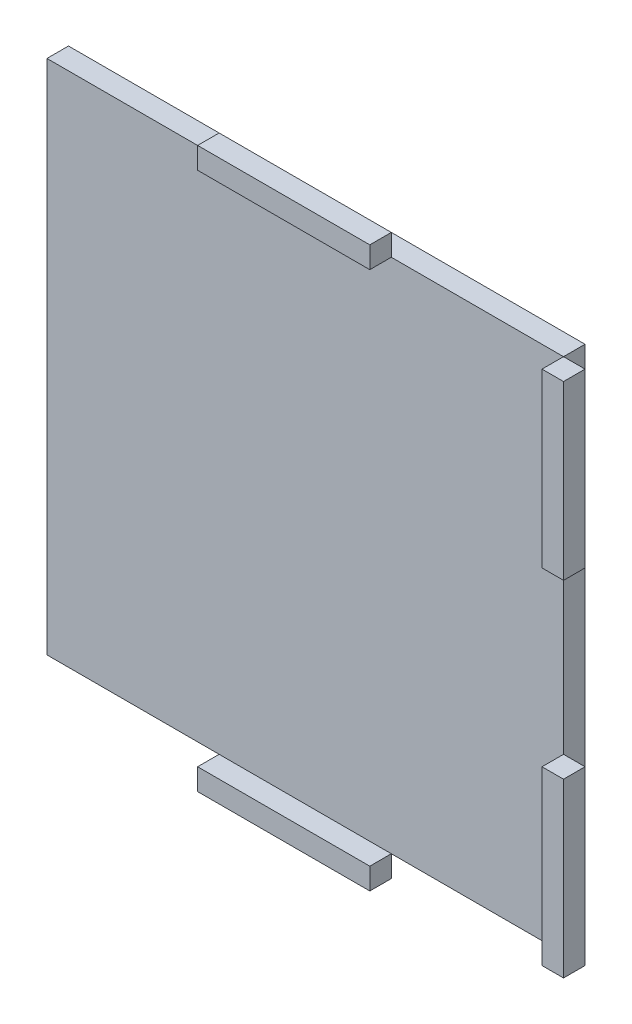
SolidWorks part; units mm, degrees
ref_plane "Front Plane" through (0, 0, 0) normal (0, 0, 1) x (1, 0, 0)
ref_plane "Top Plane" through (0, 0, 0) normal (0, 1, 0) x (1, 0, 0)
ref_plane "Right Plane" through (0, 0, 0) normal (1, 0, 0) x (0, 0, -1)
sketch "Sketch2" plane through (0, 0, 0) normal (0, 0, 1) x (1, 0, 0)
  line L1 (-38.1, -38.1) -> (38.1, -38.1)
  line L2 (-38.1, -38.1) -> (-38.1, 38.1)
  line L3 (-38.1, 38.1) -> (38.1, 38.1)
  line L4 (38.1, -38.1) -> (38.1, 38.1)
  line L5 (-38.1, -38.1) -> (38.1, 38.1) construction
  line L6 (-38.1, 38.1) -> (38.1, -38.1) construction
  point P0 (0, 0)
  dimension "D1" = 76.2
  dimension "D2" = 76.2
extrude "Boss-Extrude1" add sketch "Sketch2" along normal blind 3.175
sketch "Sketch4" plane through (0, 0, 3.175) normal (0, 0, 1) x (1, 0, 0)
  line L0 (-38.1, -38.1) -> (38.1, -38.1) construction
  line L9 (-12.7, -38.1) -> (12.7, -38.1)
  line L10 (-12.7, -38.1) -> (-12.7, -41.275)
  line L11 (-12.7, -41.275) -> (12.7, -41.275)
  line L12 (12.7, -38.1) -> (12.7, -41.275)
  line L13 (38.1, 38.1) -> (-38.1, 38.1) construction
  line L22 (38.1, 38.1) -> (41.275, 38.1)
  line L23 (38.1, 38.1) -> (38.1, 12.7)
  line L24 (38.1, 12.7) -> (41.275, 12.7)
  line L25 (41.275, 38.1) -> (41.275, 12.7)
  line L26 (38.1, -38.1) -> (41.275, -38.1)
  line L27 (38.1, -38.1) -> (38.1, -12.7)
  line L28 (38.1, -12.7) -> (41.275, -12.7)
  line L29 (41.275, -38.1) -> (41.275, -12.7)
  line L30 (-12.7, 38.1) -> (12.7, 38.1)
  line L31 (-12.7, 38.1) -> (-12.7, 41.275)
  line L32 (-12.7, 41.275) -> (12.7, 41.275)
  line L33 (12.7, 38.1) -> (12.7, 41.275)
  line L34 (-38.1, 38.1) -> (-38.1, -38.1) construction
  dimension "D1" = 25.4
  dimension "D2" = 25.4
  dimension "D3" = 25.4
  dimension "D4" = 25.4
  dimension "D5" = 25.4
  dimension "D6" = 25.4
  dimension "D7" = 3.175
  dimension "D8" = 3.175
  dimension "D9" = 3.175
  dimension "D10" = 3.175
extrude "Boss-Extrude3" add sketch "Sketch4" along normal blind 3.175 separate body
